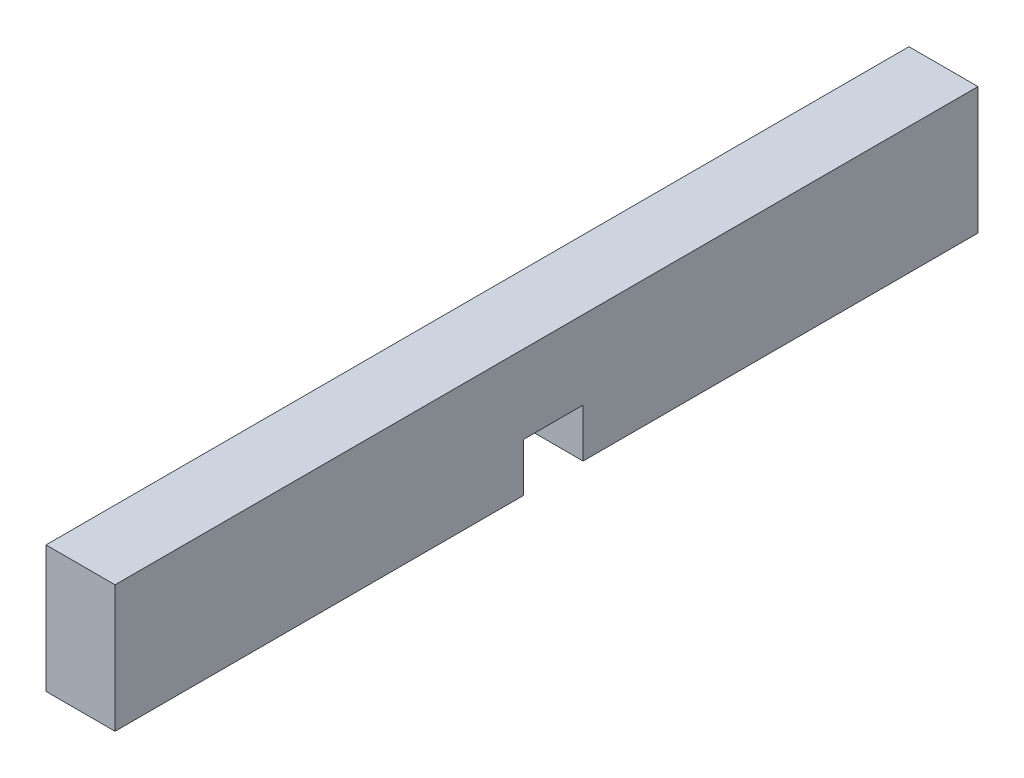
SolidWorks part; units mm, degrees
ref_plane "Front Plane" through (0, 0, 0) normal (0, 0, 1) x (1, 0, 0)
ref_plane "Top Plane" through (0, 0, 0) normal (0, 1, 0) x (1, 0, 0)
ref_plane "Right Plane" through (0, 0, 0) normal (1, 0, 0) x (0, 0, -1)
sketch "Sketch1" plane through (0, 0, 0) normal (1, 0, 0) x (0, 0, -1)
  line L1 (-29.3624, 4.318) -> (29.3624, 4.318)
  line L2 (-29.3624, 4.318) -> (-29.3624, -4.318)
  line L3 (-29.3624, -4.318) -> (29.3624, -4.318)
  line L4 (29.3624, 4.318) -> (29.3624, -4.318)
  line L5 (-29.3624, 4.318) -> (29.3624, -4.318) construction
  line L6 (-29.3624, -4.318) -> (29.3624, 4.318) construction
  point P0 (0, 0)
  dimension "D1" = 58.7248
  dimension "D2" = 8.636
extrude "Boss-Extrude1" add sketch "Sketch1" along normal mid plane 4.699
sketch "Sketch2" plane through (2.3495, 0, 0) normal (1, 0, 0) x (0, 0, -1)
  line L0 (-29.3624, -4.318) -> (29.3624, -4.318) construction
  line L1 (-1.5748, -4.318) -> (2.4892, -4.318)
  line L2 (-1.5748, -4.318) -> (-1.5748, -1.016)
  line L3 (-1.5748, -1.016) -> (2.4892, -1.016)
  line L4 (2.4892, -4.318) -> (2.4892, -1.016)
  line L5 (-29.3624, 4.318) -> (-29.3624, -4.318) construction
  dimension "D1" = 27.7876
  dimension "D2" = 4.064
  dimension "D3" = 3.302
extrude "Cut-Extrude1" cut sketch "Sketch2" against normal blind 4.699
